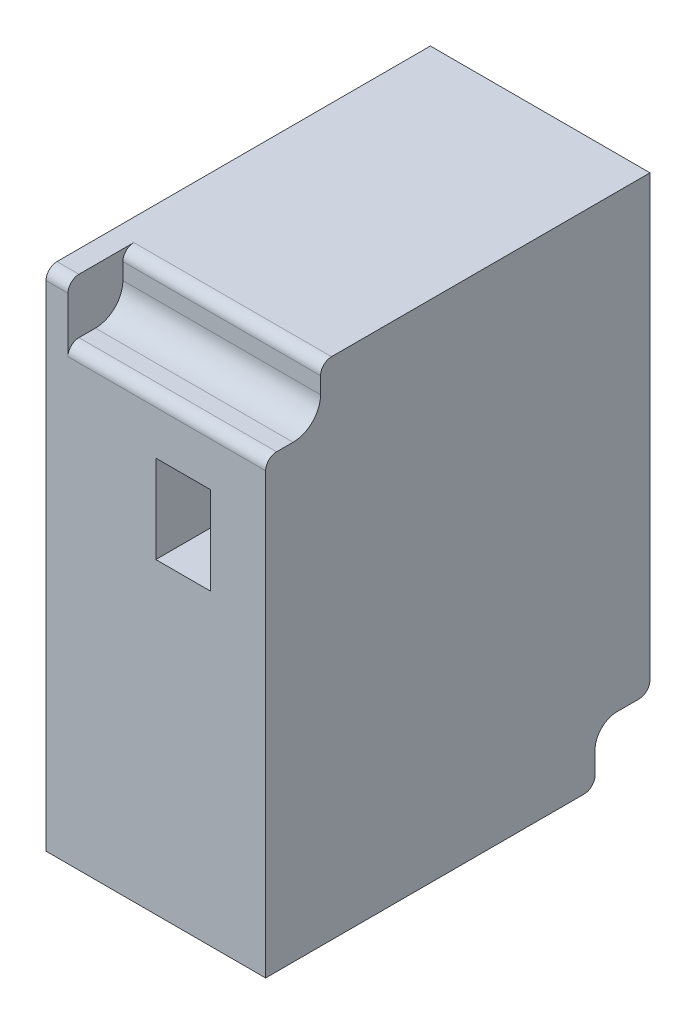
SolidWorks part; units mm, degrees
ref_plane "Front Plane" through (0, 0, 0) normal (0, 0, 1) x (1, 0, 0)
ref_plane "Top Plane" through (0, 0, 0) normal (0, 1, 0) x (1, 0, 0)
ref_plane "Right Plane" through (0, 0, 0) normal (1, 0, 0) x (0, 0, -1)
sketch "Sketch1" plane through (0, 0, 0) normal (0, 0, 1) x (1, 0, 0)
  line L0 (0, 0) -> (20, 0)
  line L1 (20, 0) -> (20, 46)
  line L2 (20, 46) -> (0, 46)
  line L3 (0, 46) -> (0, 0)
extrude "Boss-Extrude1" add sketch "Sketch1" against normal blind 35
sketch "Sketch2" plane through (0, 0, 0) normal (0, 0, 1) x (1, 0, 0)
  line L0 (10, 41) -> (10, 36) construction
  line L1 (20, 46) -> (0, 46) construction
  line L2 (10, 41) -> (2, 41)
  line L3 (2, 41) -> (2, 46)
  line L4 (2, 46) -> (20, 46)
  line L5 (20, 46) -> (20, 41)
  line L6 (20, 0) -> (20, 46) construction
  line L7 (20, 41) -> (10, 41)
  line L8 (10, 36) -> (15, 36)
  line L9 (15, 36) -> (15, 28)
  line L10 (15, 28) -> (10, 28)
  line L11 (10, 28) -> (10, 36)
extrude "Cut-Extrude1" cut sketch "Sketch2" against normal blind 5
fillet "Fillet1" radius 2.5 1 edges at (11, 41, -5)
fillet "Fillet2" radius 1 1 edges at (1, 46, 0)
fillet "Fillet3" radius 1 2 edges at (11, 41, 0) (11, 46, -5)
sketch "Sketch3" plane through (0, 0, -35) normal (0, 0, -1) x (-1, 0, 0)
  line L0 (-10, 46) -> (-10, 36) construction
  line L1 (0, 0) -> (-20, 0) construction
  line L2 (-10, 5) -> (-20, 5)
  line L3 (-20, 0) -> (-20, 46) construction
  line L4 (-10, 5) -> (-5, 5)
  line L5 (-5, 5) -> (-5, 0)
  line L6 (-5, 0) -> (-20, 0)
  line L7 (-20, 0) -> (-20, 5)
  line L8 (-20, 46) -> (0, 46) construction
  circle A1 centre (-10, 36) radius 9
  circle A2 centre (-10, 36) radius 6.5
extrude "Cut-Extrude2" cut sketch "Sketch3" against normal blind 5
fillet "Fillet4" radius 2 1 edges at (12.5, 5, -30)
fillet "Fillet5" radius 1 3 edges at (2.5, 0, -35) (12.5, 0, -30) (12.5, 5, -35)
